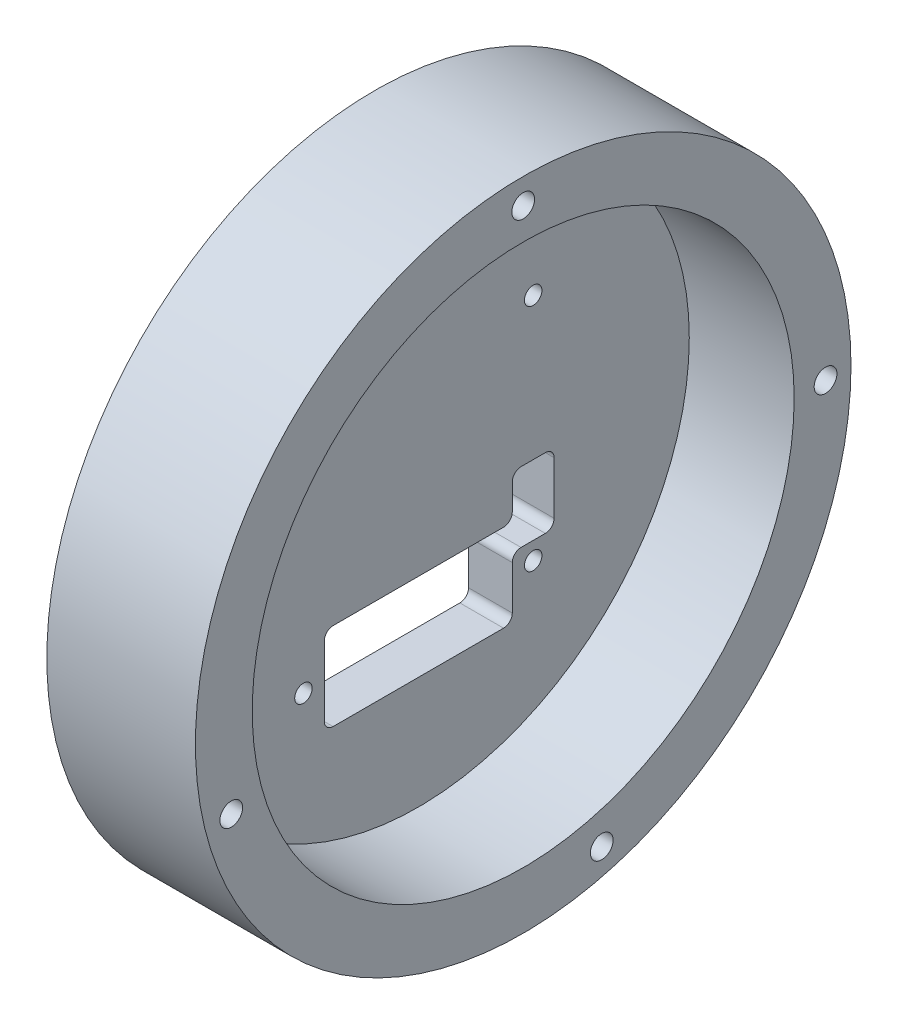
SolidWorks part; units mm, degrees
ref_plane "Front Plane" through (0, 0, 0) normal (0, 0, 1) x (1, 0, 0)
ref_plane "Top Plane" through (0, 0, 0) normal (0, 1, 0) x (1, 0, 0)
ref_plane "Right Plane" through (0, 0, 0) normal (1, 0, 0) x (0, 0, -1)
sketch "Sketch1" plane through (0, 0, 0) normal (1, 0, 0) x (0, 0, -1)
  circle A0 centre (0, 0) radius 37.5
  dimension "D1" = 75
extrude "Boss-Extrude1" add sketch "Sketch1" along normal blind 5
sketch "Sketch3" plane through (0, 0, 0) normal (-1, 0, 0) x (0, 0, 1)
  circle A0 centre (-13.14, 13.14) radius 1
  circle A1 centre (13.14, 13.14) radius 1
  circle A2 centre (13.14, -13.14) radius 1
  circle A3 centre (-13.14, -13.14) radius 1
  point P12 (0, 0)
  dimension "D1" = 2
  dimension "D2" = 13.14
  dimension "D3" = 13.14
  dimension "D4" = 4
extrude "Cut-Extrude2" cut sketch "Sketch3" against normal through all
sketch "Sketch4" plane through (5, 0, 0) normal (1, 0, 0) x (0, 0, -1)
  circle A0 centre (0, 0) radius 37.5
  circle A1 centre (0, 0) radius 31
  dimension "D1" = 75
  dimension "D2" = 62
extrude "Boss-Extrude2" add sketch "Sketch4" along normal blind 12
sketch "Sketch2" plane through (5, 0, 0) normal (1, 0, 0) x (0, 0, -1)
  line L0 (0, 34.5881) -> (0, 37.5) construction
  line L1 (8.9844, -33.4008) -> (9.7408, -36.2128) construction
  circle A1 centre (0, 34.5881) radius 1.3
  circle A2 centre (8.9844, -33.4008) radius 1.3
  circle A3 centre (0, 0) radius 37.5 construction
  circle A4 centre (34.5881, 0) radius 1.3
  circle A5 centre (-33.4008, -8.9844) radius 1.3
  point P17 (0, 0)
  dimension "D2" = 2.6
  dimension "D1" = 68.58
  dimension "D3" = 2
extrude "Cut-Extrude1" cut sketch "Sketch2" against normal through all both and the other way through all
sketch "Sketch5" plane through (5, 0, 0) normal (1, 0, 0) x (0, 0, -1)
  line L0 (-13.14, -13.14) -> (13.14, -13.14) construction
  line L1 (9.75, -8.14) -> (-9.75, -8.14)
  line L2 (10.75, -12.14) -> (10.75, -17.14)
  line L3 (9.75, -18.14) -> (-9.75, -18.14)
  line L4 (-10.75, -9.14) -> (-10.75, -17.14)
  line L5 (10.75, -8.14) -> (-10.75, -18.14) construction
  line L6 (10.75, -18.14) -> (-10.75, -8.14) construction
  line L8 (14.53, -3.14) -> (11.75, -3.14)
  line L9 (15.53, -4.14) -> (15.53, -10.14)
  line L10 (14.53, -11.14) -> (11.75, -11.14)
  line L11 (10.75, -4.14) -> (10.75, -7.14)
  line L12 (15.53, -3.14) -> (10.75, -11.14) construction
  line L13 (15.53, -11.14) -> (10.75, -3.14) construction
  arc A0 (11.75, -11.14) -> (10.75, -12.14) centre (11.75, -12.14) ccw
  arc A1 (-10.75, -9.14) -> (-9.75, -8.14) centre (-9.75, -9.14) cw
  arc A2 (-9.75, -18.14) -> (-10.75, -17.14) centre (-9.75, -17.14) cw
  arc A3 (10.75, -17.14) -> (9.75, -18.14) centre (9.75, -17.14) cw
  arc A4 (15.53, -10.14) -> (14.53, -11.14) centre (14.53, -10.14) cw
  arc A5 (10.75, -4.14) -> (11.75, -3.14) centre (11.75, -4.14) cw
  arc A6 (15.53, -4.14) -> (14.53, -3.14) centre (14.53, -4.14) ccw
  arc A7 (9.75, -8.14) -> (10.75, -7.14) centre (9.75, -7.14) ccw
  point P0 (0, -13.14)
  point P5 (13.14, -7.14)
  dimension "D5" = 1
  dimension "D6" = 1
  dimension "D1" = 10
  dimension "D2" = 21.5
  dimension "D3" = 8
  dimension "D4" = 2
extrude "Cut-Extrude3" cut sketch "Sketch5" against normal through all
sketch "Sketch6" plane through (0, 0, 0) normal (-1, 0, 0) x (0, 0, 1)
  line L0 (0, 37.5) -> (0, -37.5) construction
  line L1 (-18.75, 32.476) -> (18.75, -32.476) construction
  line L2 (-18.75, 32.476) -> (-17.145, 29.696) construction
  line L3 (17.145, -29.696) -> (18.75, -32.476) construction
  circle A0 centre (0, 0) radius 37.5 construction
  circle A1 centre (-17.145, 29.696) radius 1.5
  circle A2 centre (17.145, -29.696) radius 1.5
  circle A3 centre (29.696, 17.145) radius 1.5
  circle A4 centre (17.145, -29.696) radius 1.5 [skipped]
  circle A5 centre (-29.696, -17.145) radius 1.5
  point P7 (0, 0)
  point P22 (0, 0)
  dimension "D2" = 3
  dimension "D3" = 3
  dimension "D4" = 68.58
  dimension "D1" = 30
  dimension "D5" = 4
extrude "Cut-Extrude4" [suppressed] cut sketch "Sketch6" against normal through all
